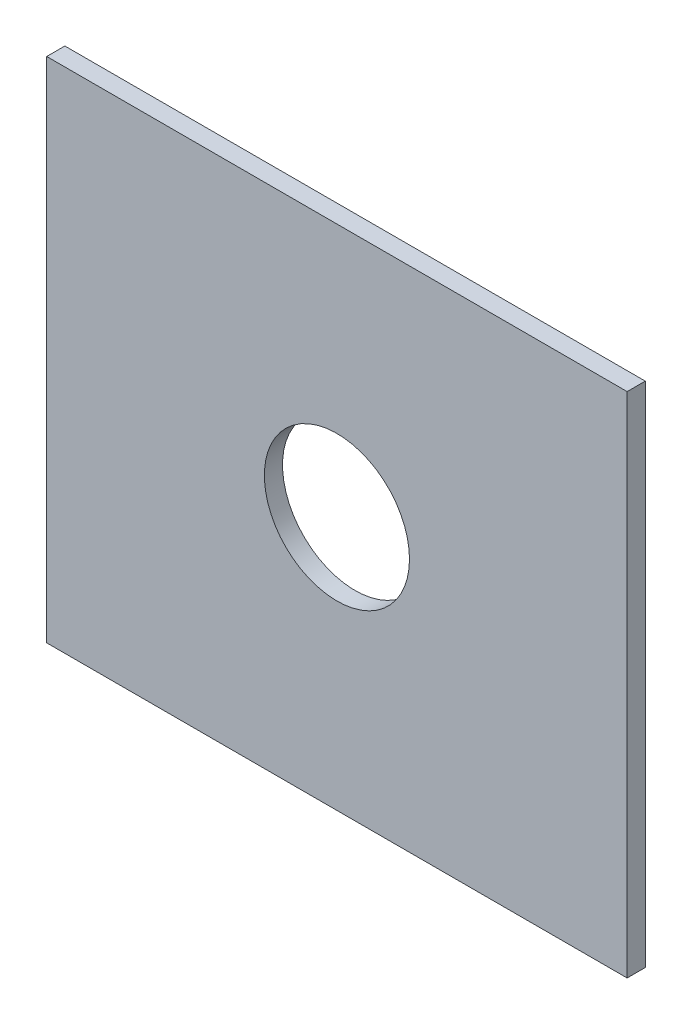
SolidWorks part; units mm, degrees
ref_plane "Front" through (0, 0, 0) normal (0, 0, 1) x (1, 0, 0)
ref_plane "Top" through (0, 0, 0) normal (0, 1, 0) x (1, 0, 0)
ref_plane "Right" through (0, 0, 0) normal (1, 0, 0) x (0, 0, -1)
sketch "Sketch1" plane through (0, 0, 0) normal (0, 0, 1) x (1, 0, 0)
  line L1 (25.4, 11.1125) -> (-25.4, 11.1125)
  line L2 (25.4, 11.1125) -> (25.4, 55.5625)
  line L3 (25.4, 55.5625) -> (-25.4, 55.5625)
  line L4 (-25.4, 11.1125) -> (-25.4, 55.5625)
  line L5 (-25.4, 33.3375) -> (25.4, 33.3375) construction
  circle A0 centre (0, 33.3375) radius 7.9375 construction
  point P8 (0, 33.3375)
  dimension "D1" = 44.45
  dimension "D2" = 50.8
extrude "Extrude1" add sketch "Sketch1" along normal blind 1.5875
sketch "Sketch2" plane through (0, 0, 1.5875) normal (0, 0, 1) x (1, 0, 0)
  circle A0 centre (0, 33.3375) radius 6.35
  circle A1 centre (0, 33.3375) radius 7.9375 construction
  dimension "D1" = 12.7
extrude "Cut-Extrude1" cut sketch "Sketch2" against normal through all
